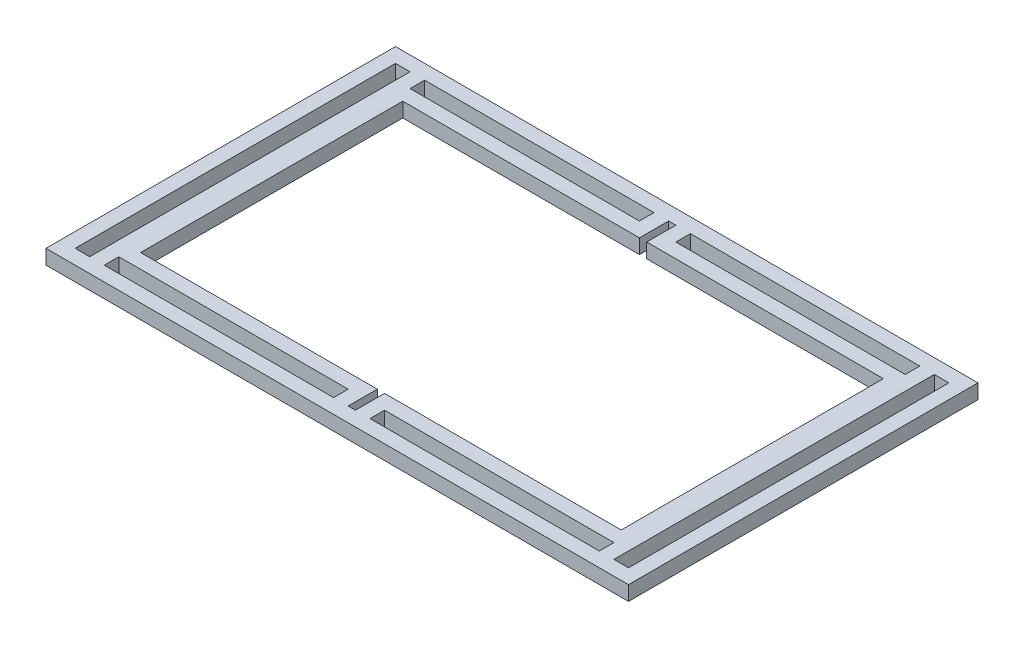
SolidWorks part; units mm, degrees
ref_plane "Front Plane" through (0, 0, 0) normal (0, 0, 1) x (1, 0, 0)
ref_plane "Top Plane" through (0, 0, 0) normal (0, 1, 0) x (1, 0, 0)
ref_plane "Right Plane" through (0, 0, 0) normal (1, 0, 0) x (0, 0, -1)
sketch "Sketch1" plane through (0, 0, 0) normal (0, 1, 0) x (1, 0, 0)
  line L0 (0, 76.2) -> (0, -76.2) construction
  line L1 (127, -76.2) -> (-127, -76.2)
  line L2 (127, -76.2) -> (127, 76.2)
  line L3 (127, 76.2) -> (-127, 76.2)
  line L4 (-127, -76.2) -> (-127, 76.2)
  line L5 (127, -76.2) -> (-127, 76.2) construction
  line L6 (127, 76.2) -> (-127, -76.2) construction
  line L11 (120.65, -69.85) -> (114.3, -69.85)
  line L12 (120.65, -69.85) -> (120.65, 69.85)
  line L13 (120.65, 69.85) -> (114.3, 69.85)
  line L14 (114.3, -69.85) -> (114.3, 69.85)
  line L15 (120.65, -69.85) -> (114.3, 69.85) construction
  line L16 (120.65, 69.85) -> (114.3, -69.85) construction
  line L17 (1.5875, -69.85) -> (-1.5875, -69.85)
  line L18 (1.5875, -69.85) -> (1.5875, 69.85)
  line L19 (1.5875, 69.85) -> (-1.5875, 69.85)
  line L20 (-1.5875, -69.85) -> (-1.5875, 69.85)
  line L21 (1.5875, -69.85) -> (-1.5875, 69.85) construction
  line L22 (1.5875, 69.85) -> (-1.5875, -69.85) construction
  line L23 (-120.65, -69.85) -> (-114.3, -69.85)
  line L24 (-114.3, -69.85) -> (-114.3, 69.85)
  line L25 (-120.65, -69.85) -> (-120.65, 69.85)
  line L26 (-120.65, 69.85) -> (-114.3, 69.85)
  line L27 (-127, 0) -> (127, 0) construction
  line L28 (-107.95, 69.85) -> (-7.9375, 69.85)
  line L29 (-107.95, 69.85) -> (-107.95, 63.5051)
  line L30 (-107.95, 63.5051) -> (-7.9375, 63.5051)
  line L31 (-7.9375, 69.85) -> (-7.9375, 63.5051)
  line L36 (7.9375, -63.5102) -> (107.95, -63.5102)
  line L37 (7.9375, -63.5102) -> (7.9375, -69.8551)
  line L38 (7.9375, -69.8551) -> (107.95, -69.8551)
  line L39 (107.95, -63.5102) -> (107.95, -69.8551)
  line L40 (7.9375, 63.5051) -> (107.95, 63.5051)
  line L41 (7.9375, 63.5051) -> (7.9375, 69.85)
  line L42 (7.9375, 69.85) -> (107.95, 69.85)
  line L43 (107.95, 63.5051) -> (107.95, 69.85)
  line L44 (-7.9375, -69.85) -> (-7.9375, -63.5051)
  line L45 (-107.95, -69.85) -> (-107.95, -63.5051)
  line L46 (-107.95, -69.85) -> (-7.9375, -69.85)
  line L47 (-107.95, -63.5051) -> (-7.9375, -63.5051)
  line L56 (-120.65, -57.15) -> (-114.3, -57.15)
  line L57 (-120.65, -44.45) -> (-114.3, -44.45)
  line L58 (-120.65, -31.75) -> (-114.3, -31.75)
  line L59 (-120.65, -19.05) -> (-114.3, -19.05)
  line L60 (-120.65, -6.35) -> (-114.3, -6.35)
  line L61 (-120.65, 6.35) -> (-114.3, 6.35)
  line L62 (-120.65, 19.05) -> (-114.3, 19.05)
  line L63 (-120.65, 31.75) -> (-114.3, 31.75)
  line L64 (-120.65, 44.45) -> (-114.3, 44.45)
  line L65 (-120.65, 57.15) -> (-114.3, 57.15)
  line L78 (120.65, -57.15) -> (114.3, -57.15)
  line L79 (120.65, -44.45) -> (114.3, -44.45)
  line L80 (120.65, -31.75) -> (114.3, -31.75)
  line L81 (120.65, -19.05) -> (114.3, -19.05)
  line L82 (120.65, -6.35) -> (114.3, -6.35)
  line L83 (120.65, 6.35) -> (114.3, 6.35)
  line L84 (120.65, 19.05) -> (114.3, 19.05)
  line L85 (120.65, 31.75) -> (114.3, 31.75)
  line L86 (120.65, 44.45) -> (114.3, 44.45)
  line L87 (120.65, 57.15) -> (114.3, 57.15)
  point P0 (0, 0)
  point P6 (117.475, 0)
  point P12 (0, 0)
  point P39 (107.95, -66.6826)
  point P86 (-117.475, 19.05)
  dimension "D1" = 254
  dimension "D2" = 152.4
  dimension "D3" = 6.35
  dimension "D4" = 6.35
  dimension "D5" = 6.35
  dimension "D6" = 6.35
  dimension "D7" = 6.35
  dimension "D8" = 3.175
  dimension "D9" = 6.35
  dimension "D10" = 6.35
  dimension "D11" = 6.3449
  dimension "D14" = 6.3449
  dimension "D15" = 6.35
  dimension "D16" = 6.35
  dimension "D17" = 6.35
  dimension "D18" = 6.35
  dimension "D19" = 6.3449
  dimension "D33" = 12.7
  dimension "D34" = 12.7
  dimension "D35" = 12.7
  dimension "D36" = 12.7
  dimension "D37" = 12.7
  dimension "D38" = 12.7
  dimension "D39" = 12.7
  dimension "D40" = 12.7
  dimension "D41" = 12.7
  dimension "D42" = 12.7
  dimension "D43" = 6.3449
  dimension "D44" = 6.35
  dimension "D45" = 6.35
extrude "Boss-Extrude1" add sketch "Sketch1" along normal blind 6.35 contours L4 L1 L2 L3 L43 L40 L41 L42 L11 L14 L13 L12 L17 L20 L19 L18 L25
sketch "Sketch2" plane through (0, 0, 0) normal (0, 1, 0) x (1, 0, 0)
  line L1 (104.775, -57.15) -> (-104.775, -57.15)
  line L2 (104.775, -57.15) -> (104.775, 57.15)
  line L3 (104.775, 57.15) -> (-104.775, 57.15)
  line L4 (-104.775, -57.15) -> (-104.775, 57.15)
  line L5 (104.775, -57.15) -> (-104.775, 57.15) construction
  line L6 (104.775, 57.15) -> (-104.775, -57.15) construction
  point P0 (0, 0)
  dimension "D1" = 114.3
  dimension "D2" = 209.55
extrude "Cut-Extrude1" cut sketch "Sketch2" against normal blind 127 and the other way blind 65.278 contours L2 L1 L4 L3
